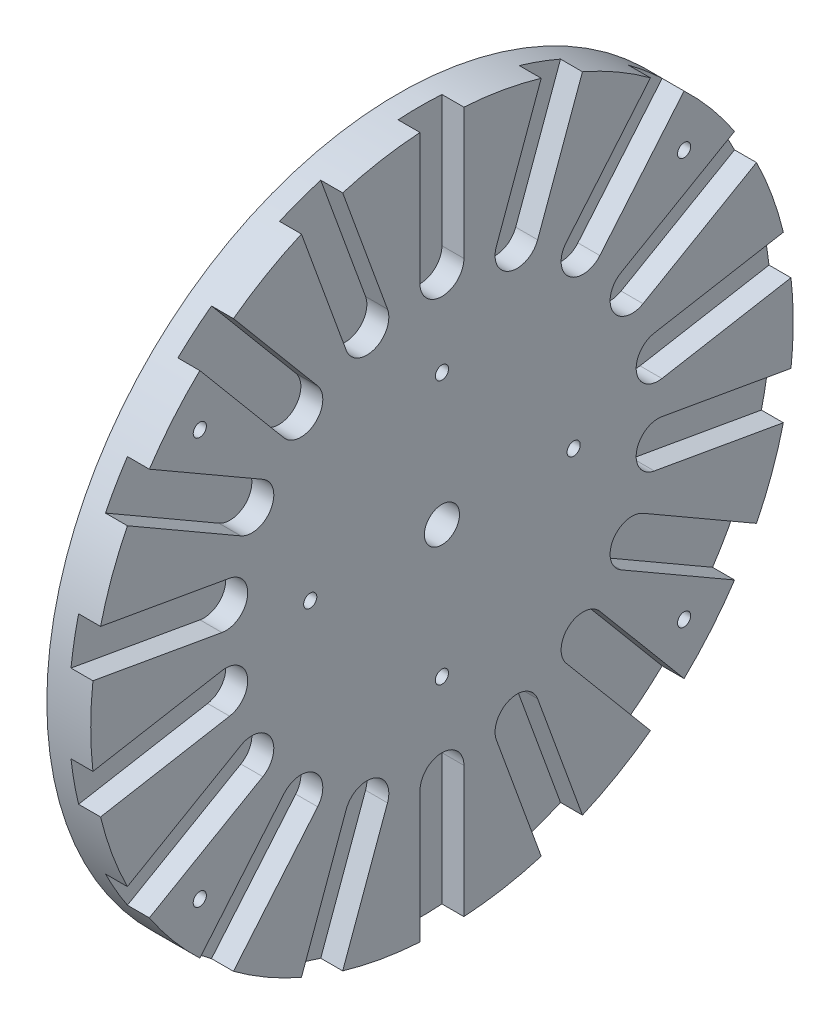
SolidWorks part; units mm, degrees
ref_plane "Front Plane" through (0, 0, 0) normal (0, 0, 1) x (1, 0, 0)
ref_plane "Top Plane" through (0, 0, 0) normal (0, 1, 0) x (1, 0, 0)
ref_plane "Right Plane" through (0, 0, 0) normal (1, 0, 0) x (0, 0, -1)
sketch "Sketch1" plane through (0, 0, 0) normal (0, 0, 1) x (1, 0, 0)
  line L0 (0, 4) -> (0, 80)
  line L1 (0, 80) -> (-10, 80)
  line L2 (-10, 80) -> (-10, 15)
  line L3 (-10, 15) -> (-25, 15)
  line L4 (-25, 15) -> (-25, 4)
  line L6 (-25, 4) -> (0, 4)
  line L7 (0, 0) -> (-22.8797, 0) construction
  dimension "D1" = 80
  dimension "D2" = 4
  dimension "D3" = 10
  dimension "D4" = 15
revolve "Revolve2" add sketch "Sketch1" angle 360 about L7
sketch "Sketch2" plane through (0, 0, 0) normal (1, 0, 0) x (0, 0, -1)
  line L0 (0, 0) -> (0, 55) construction
  line L3 (5, 50) -> (5, 80)
  line L4 (5, 80) -> (-5, 80)
  line L5 (-5, 50) -> (-5, 80)
  arc A1 (-5, 50) -> (5, 50) centre (0, 50) ccw
  dimension "D1" = 10
  dimension "D2" = 30
extrude "Cut-Extrude1" cut sketch "Sketch2" against normal blind 5
pattern_circular "CirPattern1" count 18 over 360 about axis through (0, 0, 0) along (1, 0, 0) of "Cut-Extrude1"
sketch "Sketch4" plane through (0, 0, 0) normal (1, 0, 0) x (0, 0, -1)
  line L0 (-55.1552, 46.2807) -> (0, 0) construction
  line L1 (0, 0) -> (55.1552, -46.2807) construction
  line L2 (55.1552, 46.2807) -> (-55.1552, -46.2807) construction
  line L3 (70.8769, 0) -> (-70.8769, 0) construction
  circle A0 centre (-55.1552, 46.2807) radius 1.5
  circle A1 centre (55.1552, 46.2807) radius 1.5
  circle A3 centre (55.1552, -46.2807) radius 1.5
  circle A4 centre (-55.1552, -46.2807) radius 1.5
  circle A5 centre (0, 30) radius 1.5
  circle A6 centre (0, 0) radius 4 construction
  circle A7 centre (30, 0) radius 1.5
  circle A8 centre (0, -30) radius 1.5
  circle A9 centre (-30, 0) radius 1.5
  point P8 (0, 0)
  point P11 (0, 0)
  dimension "D1" = 3
  dimension "D2" = 72
  dimension "D3" = 72
  dimension "D5" = 30
  dimension "D9" = 3
  dimension "D4" = 72
  dimension "D6" = 80
  dimension "D7" = 40
  dimension "D8" = 4
extrude "Cut-Extrude3" cut sketch "Sketch4" against normal blind 5
